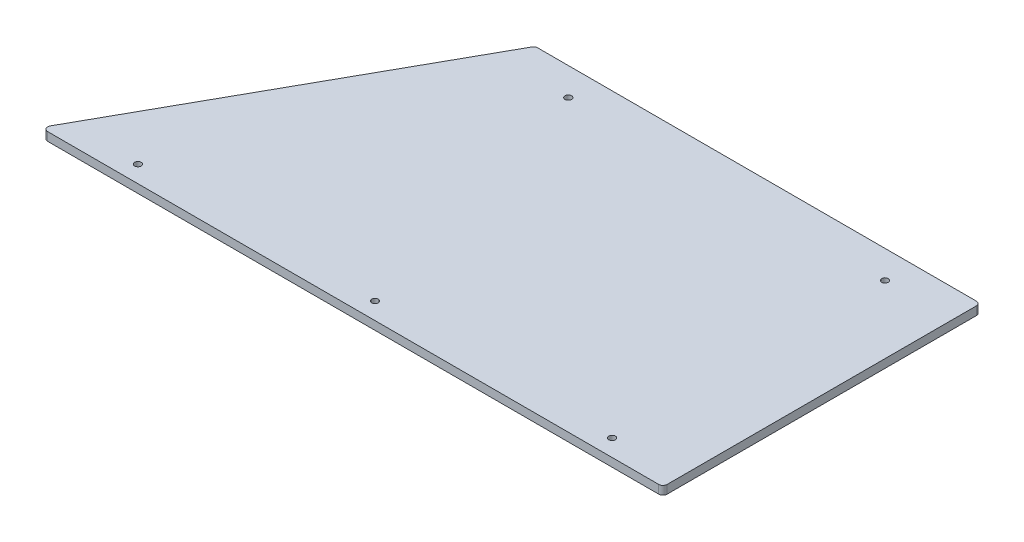
SolidWorks part; units mm, degrees
material "PE High Density"
ref_plane "Front Plane" through (0, 0, 0) normal (0, 0, 1) x (1, 0, 0)
ref_plane "Top Plane" through (0, 0, 0) normal (0, 1, 0) x (1, 0, 0)
ref_plane "Right Plane" through (0, 0, 0) normal (1, 0, 0) x (0, 0, -1)
sketch "Sketch1" plane through (0, 0, 0) normal (0, 1, 0) x (1, 0, 0)
  line L0 (0, 0) -> (132.811, 238.125)
  line L1 (132.811, 238.125) -> (466.725, 238.125)
  line L2 (466.725, 238.125) -> (466.725, 0)
  line L3 (466.725, 0) -> (0, 0)
  circle A0 centre (415.925, 217.297) radius 2.4574
  circle A1 centre (415.925, 12.7) radius 2.4574
  circle A2 centre (238.125, 12.7) radius 2.4575
  circle A3 centre (60.325, 12.7) radius 2.4574
  circle A4 centre (178.4494, 217.297) radius 2.4574
  dimension "D5" = 4.9149
  dimension "D6" = 12.7
  dimension "D8" = 177.8
  dimension "D1" = 466.725
  dimension "D2" = 238.125
  dimension "D3" = 60.85
  dimension "D4" = 204.597
  dimension "D7" = 50.8
  dimension "D9" = 177.8
  dimension "D10" = 237.4756
extrude "Boss-Extrude1" add sketch "Sketch1" along normal blind 6.35
fillet "Fillet1" radius 3.175 4 edges at (0, 3.175, 0) (132.811, 3.175, -238.125) (466.725, 3.175, -238.125) (466.725, 3.175, 0)
